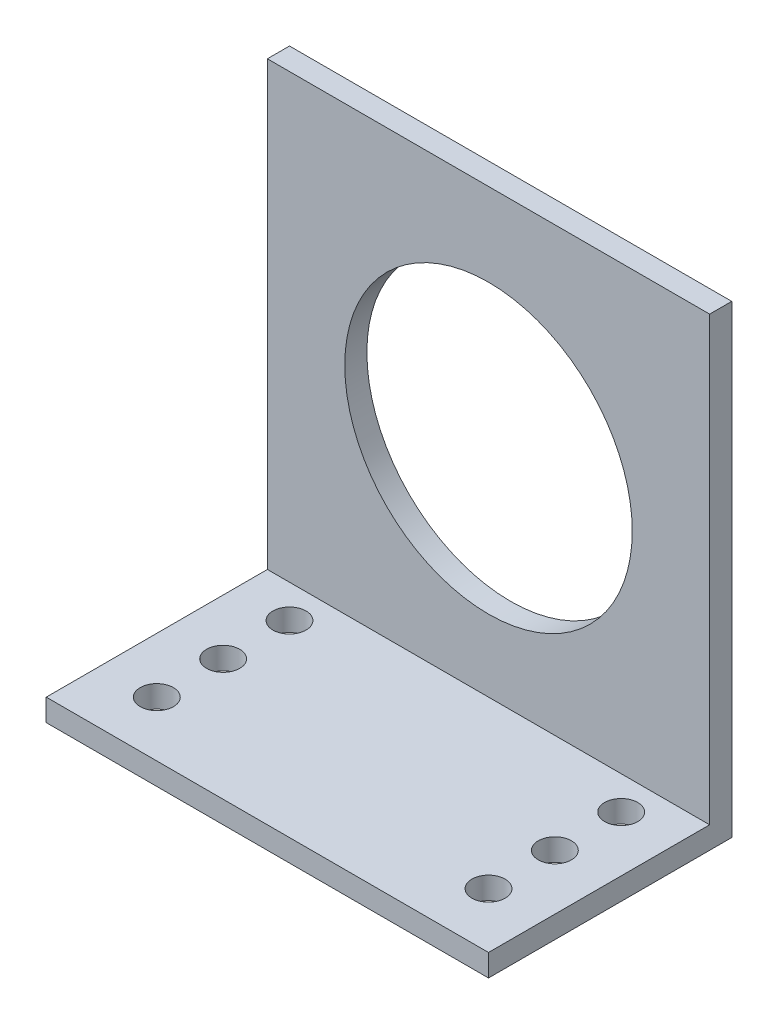
SolidWorks part; units mm, degrees
material "3003 Alloy"
ref_plane "Front Plane" through (0, 0, 0) normal (0, 0, 1) x (1, 0, 0)
ref_plane "Top Plane" through (0, 0, 0) normal (0, 1, 0) x (1, 0, 0)
ref_plane "Right Plane" through (0, 0, 0) normal (1, 0, 0) x (0, 0, -1)
sketch "Sketch2" plane through (0, 0, 0) normal (1, 0, 0) x (0, 0, -1)
  line L0 (0, 0) -> (22, 0)
  line L1 (0, 0) -> (20, 0)
  line L2 (0, 0) -> (0, 2)
  line L3 (0, 2) -> (20, 2)
  line L4 (22, 0) -> (22, 42)
  line L5 (22, 42) -> (20, 42)
  line L6 (20, 2) -> (20, 42)
  line L7 (20, 42) -> (22, 42)
  line L8 (22, 2) -> (22, 42)
  line L9 (20, 42) -> (20, 2)
  line L10 (20, 2) -> (0, 2)
  line L11 (20, 0) -> (22, 0)
  line L12 (22, 2) -> (22, 0)
  line L13 (0, 2) -> (0, 0)
extrude "Boss-Extrude1" add sketch "Sketch2" along normal blind 40 contours L6 L5 L4 L0 L2 L3
sketch "Sketch3" plane through (0, 0, -20) normal (0, 0, 1) x (1, 0, 0)
  circle A0 centre (20, 21.5) radius 13
extrude "Cut-Extrude1" cut sketch "Sketch3" against normal through all
sketch "Sketch4" plane through (0, 2, 0) normal (0, 1, 0) x (1, 0, 0)
  circle A0 centre (35, 5) radius 1.5
  circle A1 centre (5, 5) radius 1.5
  circle A2 centre (5, 11) radius 1.5
  circle A3 centre (5, 17) radius 1.5
  circle A4 centre (35, 11) radius 1.5
  circle A5 centre (35, 17) radius 1.5
  dimension "D1" = 2
  dimension "D2" = 3
extrude "Cut-Extrude2" cut sketch "Sketch4" against normal through all
